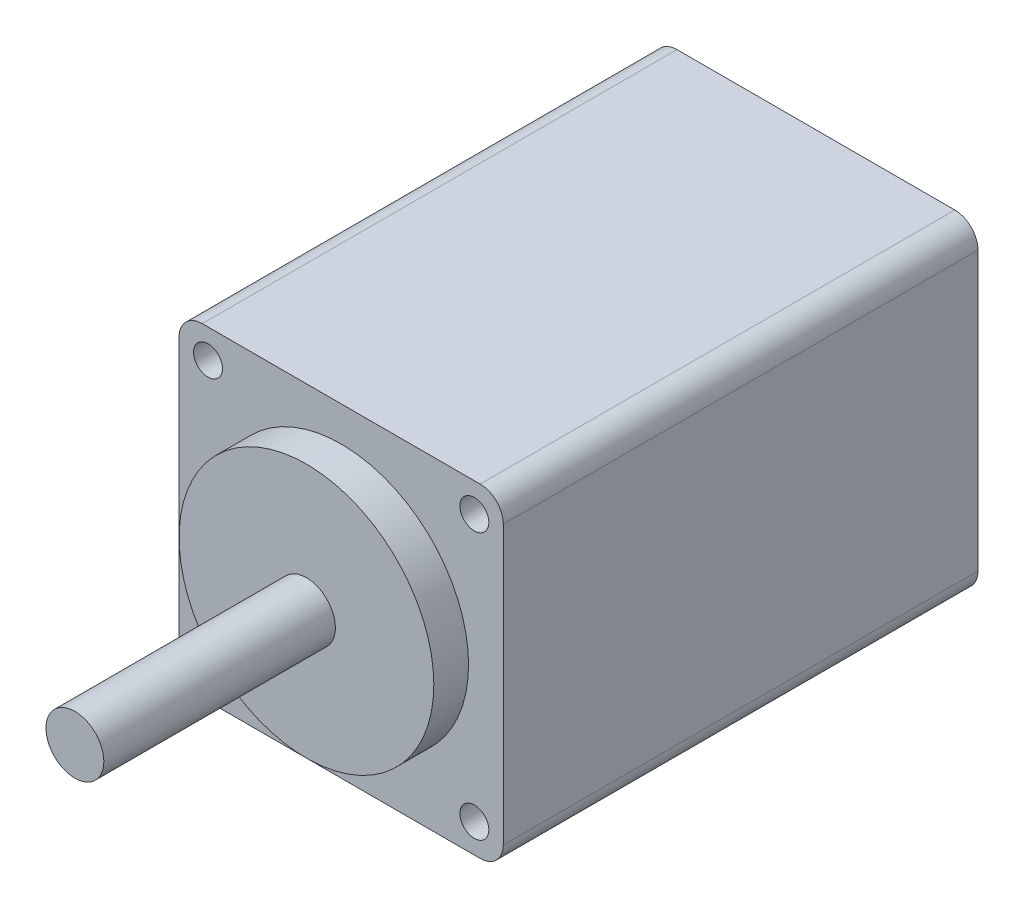
SolidWorks part; units mm, degrees
ref_plane "前视基准面" through (0, 0, 0) normal (0, 0, 1) x (1, 0, 0)
ref_plane "上视基准面" through (0, 0, 0) normal (0, 1, 0) x (1, 0, 0)
ref_plane "右视基准面" through (0, 0, 0) normal (1, 0, 0) x (0, 0, -1)
sketch "草图1" plane through (0, 0, 0) normal (0, 0, 1) x (1, 0, 0)
  line L0 (-14, 0) -> (14, 0) construction
  line L1 (-14, 14) -> (14, 14)
  line L2 (-14, 14) -> (-14, -14)
  line L3 (-14, -14) -> (14, -14)
  line L4 (14, 14) -> (14, -14)
  line L5 (-14, 14) -> (14, -14) construction
  line L6 (-14, -14) -> (14, 14) construction
  line L7 (0, 14) -> (0, -14) construction
  circle A0 centre (-11.5, 11.5) radius 1.25
  circle A2 centre (11.5, 11.5) radius 1.25
  circle A3 centre (11.5, -11.5) radius 1.25
  circle A4 centre (-11.5, -11.5) radius 1.25
  point P0 (0, 0)
  dimension "D3" = 2.5
  dimension "D4" = 23
  dimension "D1" = 28
  dimension "D2" = 28
extrude "凸台-拉伸1" add sketch "草图1" along normal blind 41
sketch "草图2" plane through (0, 0, 41) normal (0, 0, 1) x (1, 0, 0)
  circle A0 centre (0, 0) radius 11
  dimension "D1" = 22
extrude "凸台-拉伸2" add sketch "草图2" along normal blind 3
sketch "草图3" plane through (0, 0, 44) normal (0, 0, 1) x (1, 0, 0)
  circle A0 centre (0, 0) radius 2.5
  dimension "D1" = 5
extrude "凸台-拉伸3" add sketch "草图3" along normal blind 20
fillet "圆角1" radius 2 4 edges at (-14, -14, 20.5) (14, -14, 20.5) (14, 14, 20.5) (-14, 14, 20.5)
sketch "草图4" plane through (0, 0, 64) normal (0, 0, 1) x (1, 0, 0)
  circle A0 centre (0, 0) radius 1.0594 construction
